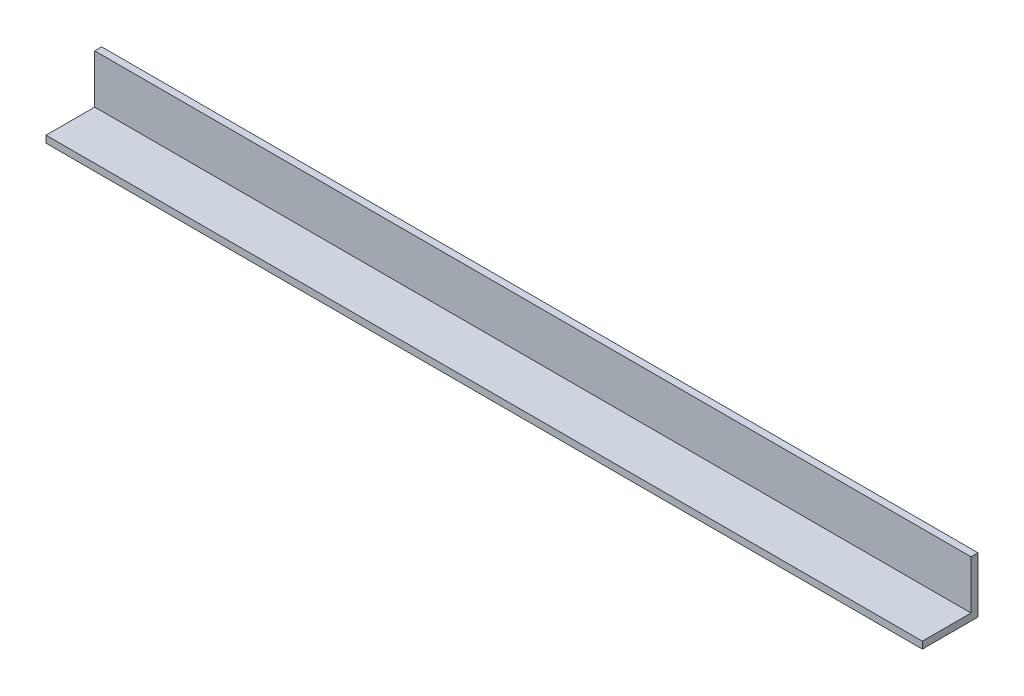
SolidWorks part; units mm, degrees
ref_plane "Alzado" through (0, 0, 0) normal (0, 0, 1) x (1, 0, 0)
ref_plane "Planta" through (0, 0, 0) normal (0, 1, 0) x (1, 0, 0)
ref_plane "Vista lateral" through (0, 0, 0) normal (1, 0, 0) x (0, 0, -1)
sketch "Croquis1" plane through (0, 0, 0) normal (1, 0, 0) x (0, 0, -1)
  line L0 (0, 25.4) -> (0, 0)
  line L1 (0, 0) -> (-25.4, 0)
  line L2 (-25.4, 0) -> (-25.4, 3.175)
  line L3 (-25.4, 3.175) -> (-3.175, 3.175)
  line L4 (-3.175, 3.175) -> (-3.175, 25.4)
  line L5 (-3.175, 25.4) -> (0, 25.4)
  dimension "D1" = 25.4
  dimension "D2" = 25.4
  dimension "D3" = 3.175
  dimension "D4" = 3.175
extrude "Saliente-Extruir1" add sketch "Croquis1" along normal blind 400
